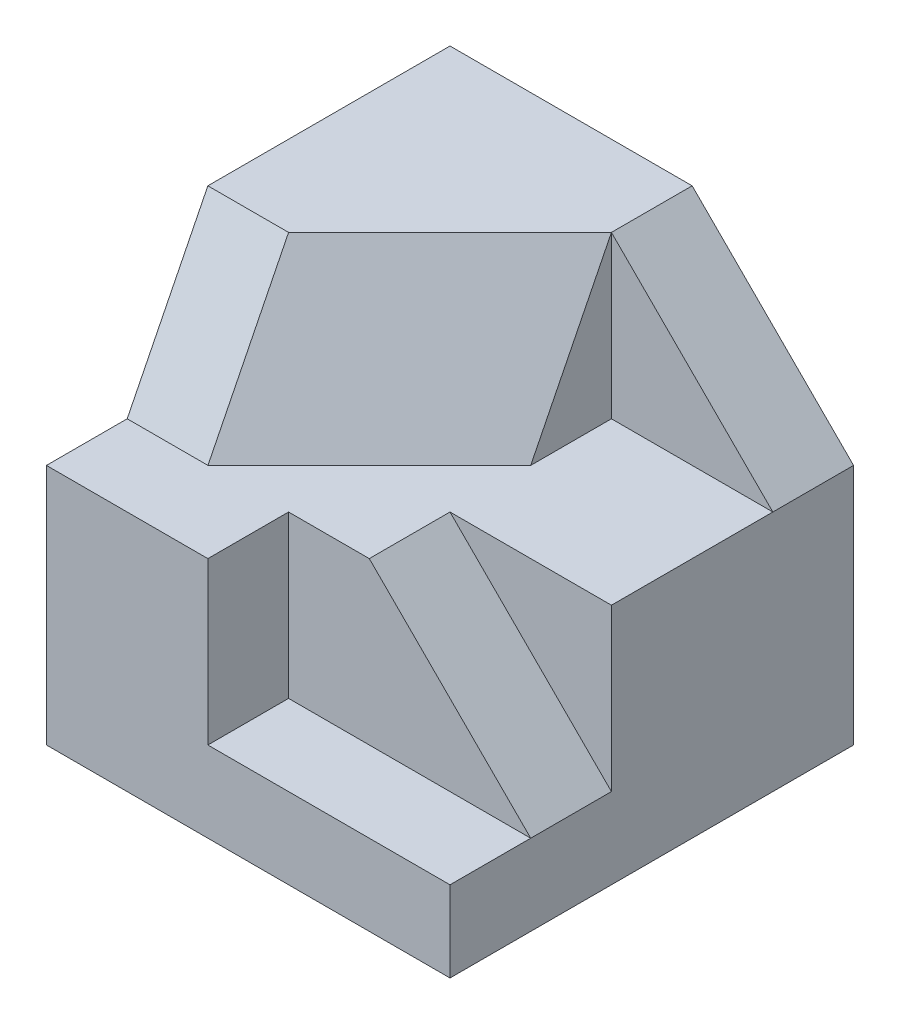
SolidWorks part; units mm, degrees
ref_plane "Front Plane" through (0, 0, 0) normal (0, 0, 1) x (1, 0, 0)
ref_plane "Top Plane" through (0, 0, 0) normal (0, 1, 0) x (1, 0, 0)
ref_plane "Right Plane" through (0, 0, 0) normal (1, 0, 0) x (0, 0, -1)
sketch "Sketch1" plane through (0, 0, 0) normal (0, 0, 1) x (1, 0, 0)
  line L1 (2.5, -2.5) -> (-2.5, -2.5)
  line L2 (2.5, -2.5) -> (2.5, 2.5)
  line L3 (2.5, 2.5) -> (-2.5, 2.5)
  line L4 (-2.5, -2.5) -> (-2.5, 2.5)
  line L5 (2.5, -2.5) -> (-2.5, 2.5) construction
  line L6 (2.5, 2.5) -> (-2.5, -2.5) construction
  point P0 (0, 0)
  dimension "D1" = 5
  dimension "D2" = 5
extrude "Boss-Extrude1" add sketch "Sketch1" along normal blind 5
sketch "Sketch3" plane through (0, 2.5, 0) normal (0, 1, 0) x (1, 0, 0)
  line L0 (-2.5, -5) -> (-2.5, -3.9995)
  line L1 (-2.5, -5) -> (-2.5, 0) construction
  line L2 (-2.5, -5) -> (2.5, -5)
  line L3 (2.5, -5) -> (2.5, -1)
  line L5 (2.5, -5) -> (2.5, 0) construction
  line L6 (2.5, -1) -> (0.5, -1)
  line L7 (0.5, -1) -> (0.5, -3)
  line L8 (0.5, -3) -> (-0.5, -3)
  line L9 (-0.5, -3) -> (-0.5, -3.9995)
  line L10 (-0.5, -3.9995) -> (-2.5, -3.9995)
  dimension "D1" = 1.0005
  dimension "D2" = 1
  dimension "D3" = 2
  dimension "D4" = 2
  dimension "D5" = 2
extrude "Cut-Extrude2" cut sketch "Sketch3" against normal blind 2
sketch "Sketch4" plane through (-0.5, 0, 0) normal (1, 0, 0) x (0, 0, -1)
  line L0 (-3, 2.5) -> (-3.9995, 0.5)
  line L1 (-3.9995, 0.5) -> (-3.9995, 2.5)
  line L2 (-3.9995, 2.5) -> (-3, 2.5)
extrude "Cut-Extrude3" cut sketch "Sketch4" against normal blind 2
sketch "Sketch5" plane through (0, 0, 1) normal (0, 0, 1) x (1, 0, 0)
  line L0 (0.5, 2.5) -> (2.5, 0.5)
  line L1 (2.5, 0.5) -> (2.5, 2.5)
  line L2 (0.5, 2.5) -> (2.5, 2.5)
extrude "Cut-Extrude4" cut sketch "Sketch5" against normal blind 2
sketch "Sketch6" plane through (0, 0, 5) normal (0, 0, 1) x (1, 0, 0)
  line L0 (-0.5, 0.5) -> (-0.5, -1.5)
  line L1 (-2.5, 0.5) -> (2.5, 0.5) construction
  line L2 (-0.5, -1.5) -> (2.5, -1.5)
  line L3 (2.5, -2.5) -> (2.5, 0.5) construction
  line L4 (2.5, -1.5) -> (2.5, 0.5)
  line L5 (2.5, 0.5) -> (-0.5, 0.5)
  dimension "D1" = 2
  dimension "D2" = 3
extrude "Cut-Extrude5" cut sketch "Sketch6" against normal blind 1
sketch "Sketch7" plane through (0, 0, 4) normal (0, 0, 1) x (1, 0, 0)
  line L0 (2.5, 0.5) -> (0.5, 0.5)
  line L1 (2.5, 0.5) -> (-0.5, 0.5) construction
  line L2 (2.5, 0.5) -> (0.5, 0.5) construction
  line L3 (0.5, 0.5) -> (2.5, -1.5)
  line L4 (2.5, -1.5) -> (2.5, 0.5)
  dimension "D1" = 2
extrude "Cut-Extrude6" cut sketch "Sketch7" against normal blind 1
sketch "Sketch8" plane through (0, 2.5, 0) normal (0, 1, 0) x (1, 0, 0)
  line L0 (0.5, -1) -> (-1.5, -3)
  line L1 (-2.5, -3) -> (-0.5, -3) construction
sketch "Sketch9" plane through (0.5, 0, 0) normal (1, 0, 0) x (0, 0, -1)
  line L0 (-1, 0.5) -> (-3, 0.5) construction
  point P0 (-2, 0.5)
sketch "Sketch10" plane through (0, 0.5, 0) normal (0, 1, 0) x (1, 0, 0)
  line L0 (-0.5, -3.9995) -> (-2.5, -3.9995) construction
  point P0 (-1.5, -3.9995)
ref_plane "Plane1" through (1.2222, 0.6111, 1.2222) normal (0.6667, 0.3333, 0.6667) x (0.7454, -0.2981, -0.5963)
sketch "Sketch11" plane through (1.2222, 0.6111, 1.2222) normal (0.6667, 0.3333, 0.6667) x (0.7454, -0.2981, -0.5963)
  line L0 (-0.969, 1.7889) -> (-3.6522, 0.8944)
  line L1 (-3.6522, 0.8944) -> (-3.6522, -1.3414)
  line L2 (-3.6522, -1.3414) -> (-0.969, -0.4472)
  line L3 (-0.969, -0.4472) -> (-0.969, 1.7889)
  line L4 (-2.9066, -1.3414) -> (-4.3973, -1.3414) construction
extrude "Cut-Extrude7" cut sketch "Sketch11" along normal blind 1
sketch "Sketch12" plane through (0, 0.5, 0) normal (0, 1, 0) x (1, 0, 0)
  line L0 (0.5, -2) -> (-1.5, -3.9995)
  line L1 (-1.5, -3.9995) -> (0.5, -4)
  line L2 (0.5, -4) -> (0.5, -2)
extrude "Cut-Extrude8" cut sketch "Sketch12" along normal through all
